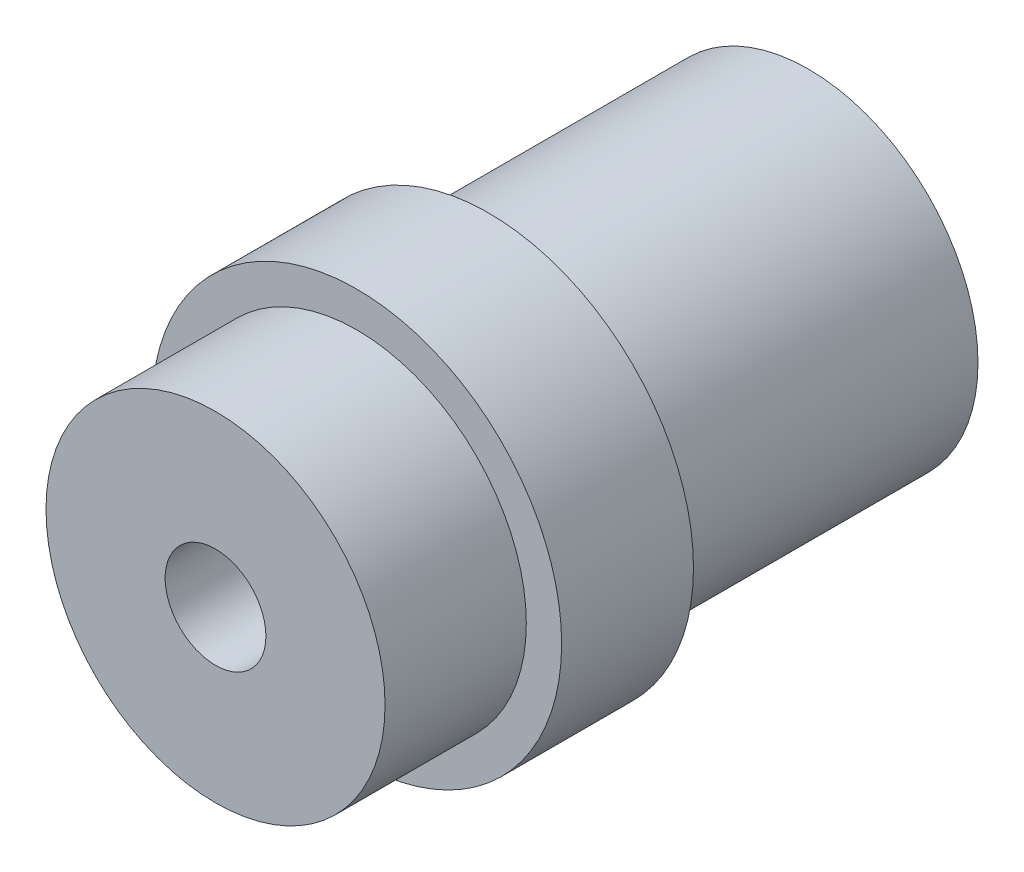
SolidWorks part; units mm, degrees
ref_plane "Front Plane" through (0, 0, 0) normal (0, 0, 1) x (1, 0, 0)
ref_plane "Top Plane" through (0, 0, 0) normal (0, 1, 0) x (1, 0, 0)
ref_plane "Right Plane" through (0, 0, 0) normal (1, 0, 0) x (0, 0, -1)
sketch "Sketch1" plane through (0, 0, 0) normal (0, 0, 1) x (1, 0, 0)
  circle A0 centre (0, 0) radius 9
  circle A1 centre (0, 0) radius 2.675
  dimension "D1" = 18
  dimension "D2" = 5.35
extrude "Boss-Extrude1" add sketch "Sketch1" along normal blind 16.98
sketch "Sketch2" plane through (0, 0, 16.98) normal (0, 0, 1) x (1, 0, 0)
  circle A0 centre (0, 0) radius 10.875
  circle A1 centre (0, 0) radius 2.675
  dimension "D1" = 21.75
extrude "Boss-Extrude2" add sketch "Sketch2" along normal blind 7
sketch "Sketch4" plane through (0, 0, 23.98) normal (0, 0, 1) x (1, 0, 0)
  circle A0 centre (0, 0) radius 9
  circle A1 centre (0, 0) radius 2.675
  dimension "D1" = 18
extrude "Boss-Extrude3" add sketch "Sketch4" along normal blind 7.5
